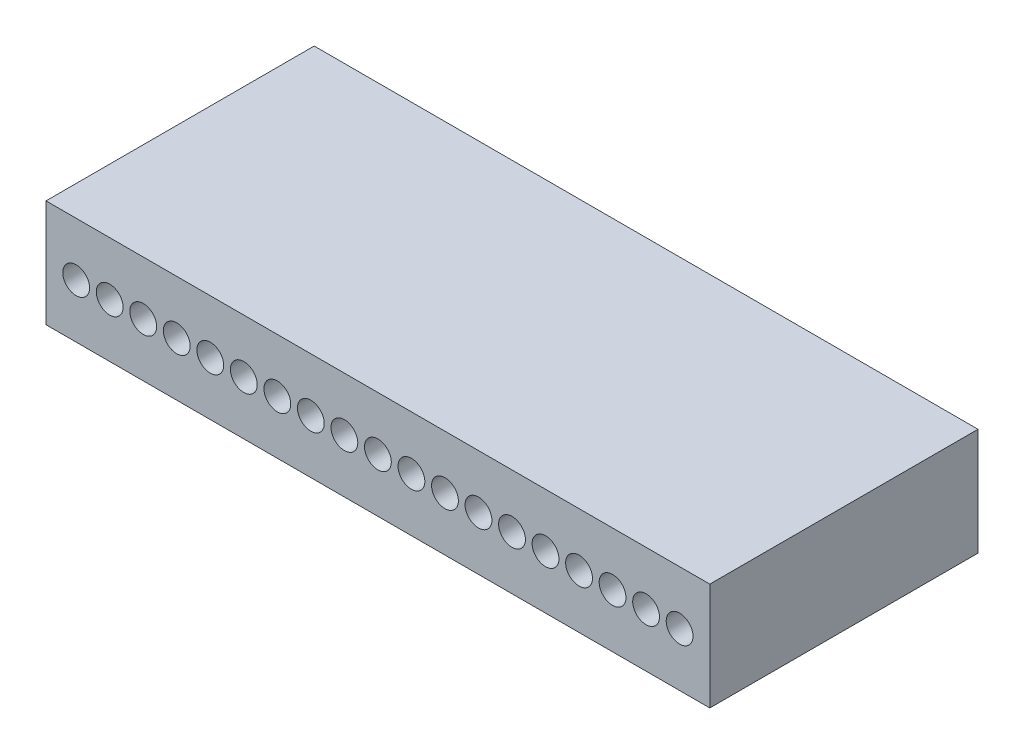
SolidWorks part; units mm, degrees
ref_plane "Front Plane" through (0, 0, 0) normal (0, 0, 1) x (1, 0, 0)
ref_plane "Top Plane" through (0, 0, 0) normal (0, 1, 0) x (1, 0, 0)
ref_plane "Right Plane" through (0, 0, 0) normal (1, 0, 0) x (0, 0, -1)
sketch "Sketch2" plane through (0, 0, 0) normal (0, 0, 1) x (1, 0, 0)
  line L1 (0, 0) -> (24.75, 0)
  line L2 (0, 0) -> (0, 4)
  line L3 (0, 4) -> (24.75, 4)
  line L4 (24.75, 0) -> (24.75, 4)
  dimension "D1" = 24.75
  dimension "D2" = 4
extrude "Boss-Extrude1" add sketch "Sketch2" along normal blind 10
sketch "Sketch3" plane through (0, 0, 10) normal (0, 0, 1) x (1, 0, 0)
  line L0 (0, 2) -> (24.75, 2) construction
  line L1 (0, 4) -> (0, 0) construction
  line L2 (24.75, 0) -> (24.75, 4) construction
  line L3 (0, 2) -> (24.75, 2) construction
  line L4 (24.75, 4) -> (0, 4) construction
  line L5 (0, 0) -> (24.75, 0) construction
  line L6 (1.125, 4) -> (1.125, 0) construction
  circle A0 centre (1.125, 2) radius 0.5
  circle A1 centre (2.375, 2) radius 0.5
  circle A2 centre (3.625, 2) radius 0.5
  circle A3 centre (4.875, 2) radius 0.5
  circle A4 centre (6.125, 2) radius 0.5
  circle A5 centre (7.375, 2) radius 0.5
  circle A6 centre (8.625, 2) radius 0.5
  circle A7 centre (9.875, 2) radius 0.5
  circle A8 centre (11.125, 2) radius 0.5
  circle A9 centre (12.375, 2) radius 0.5
  circle A10 centre (13.625, 2) radius 0.5
  circle A11 centre (14.875, 2) radius 0.5
  circle A12 centre (16.125, 2) radius 0.5
  circle A13 centre (17.375, 2) radius 0.5
  circle A14 centre (18.625, 2) radius 0.5
  circle A15 centre (19.875, 2) radius 0.5
  circle A16 centre (21.125, 2) radius 0.5
  circle A17 centre (22.375, 2) radius 0.5
  circle A18 centre (23.625, 2) radius 0.5
  circle A21 centre (24.875, 2) radius 0.5 [skipped]
  dimension "D1" = 1
  dimension "D2" = 2
  dimension "D3" = 1.125
  dimension "D5" = 1.25
  dimension "D4" = 20
extrude "Cut-Extrude1" cut sketch "Sketch3" against normal blind 5
sketch "Sketch4" plane through (0, 0, 10) normal (0, 0, 1) x (1, 0, 0)
  point P0 (1.125, 2)
  point P1 (2.375, 2)
  point P3 (3.625, 2)
  point P5 (4.875, 2)
  point P7 (6.125, 2)
  point P9 (7.375, 2)
  point P11 (8.625, 2)
  point P13 (9.875, 2)
  point P15 (11.125, 2)
  point P17 (12.375, 2)
  point P19 (13.625, 2)
  point P21 (14.875, 2)
  point P23 (16.125, 2)
  point P25 (17.375, 2)
  point P27 (18.625, 2)
  point P29 (19.875, 2)
  point P31 (21.125, 2)
  point P33 (22.375, 2)
  point P35 (23.625, 2)
